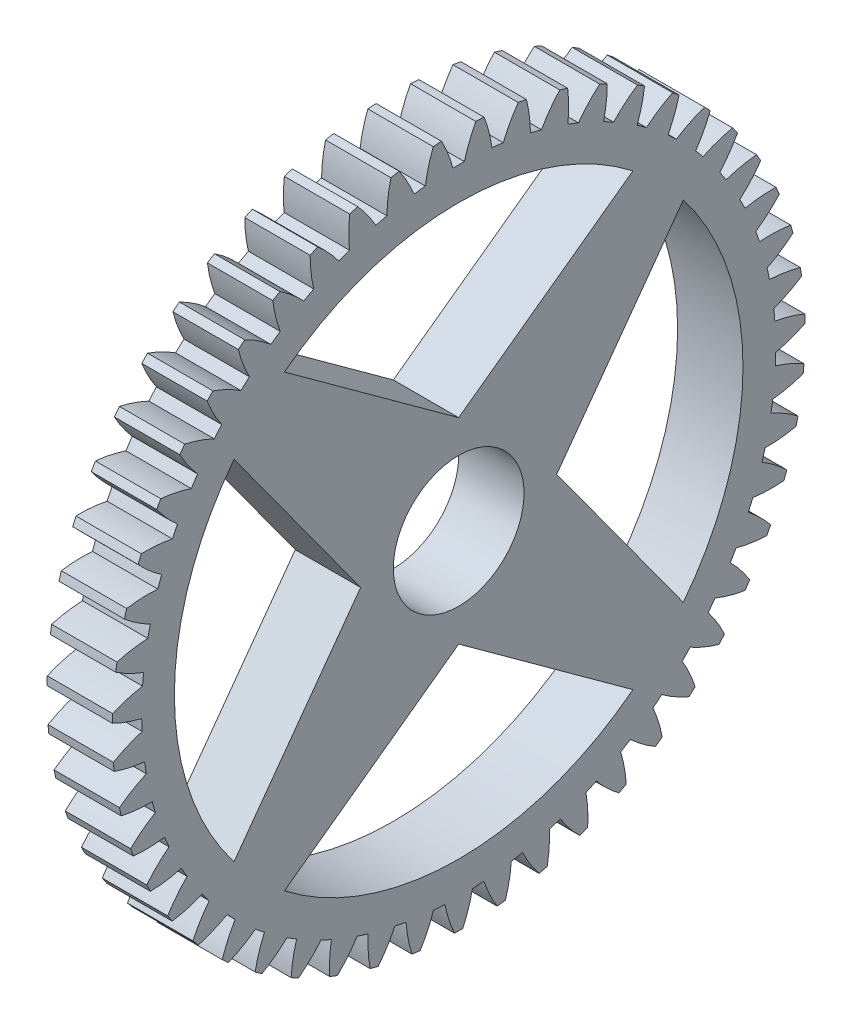
SolidWorks part; units mm, degrees
ref_plane "Plane1" through (0, 0, 0) normal (0, 0, 1) x (1, 0, 0)
ref_plane "Plane2" through (0, 0, 0) normal (0, 1, 0) x (1, 0, 0)
ref_plane "Plane3" through (0, 0, 0) normal (1, 0, 0) x (0, 0, -1)
sketch "HoldingSke" plane through (0, 0, 0) normal (0, 1, 0) x (1, 0, 0)
  line L0 (0, 0) -> (0.6293, -0.7771)
  line L1 (-15, 0) -> (100, 0) construction
  line L2 (0, 0) -> (-2.1039, 2.3779)
  line L3 (0, 0) -> (-11.863, 4.5341)
  line L4 (0, 0) -> (5.4348, 6.7114)
  line L5 (0, 0) -> (-46.8476, -17.4728)
  line L6 (0, 0) -> (-4.1448, -2.7965)
  line L7 (-2.1039, 2.3779) -> (8.6586, 51.2059)
  line L8 (-76.2, 54.61) -> (-75.3, 54.61)
  line L9 (-71.009, 38.7566) -> (-53.1078, 45.2721)
  line L10 (-76.2, 71.12) -> (104.1128, 71.12)
  line L11 (0, 0) -> (-5, 0)
  line L12 (-76.2, 101.6) -> (-76.162, 101.6)
  line L13 (24.9733, 27.94) -> (52.9518, 28.4284)
  line L14 (24.9733, 27.94) -> (24.9743, 27.94)
  line L15 (24.9733, 27.94) -> (100.4006, 29.5858)
  line L16 (-63.627, -1) -> (-12.827, -1)
  circle A0 centre (0, 0) radius 2.5
  circle A1 centre (0, 0) radius 24.249
  circle A2 centre (0, 0) radius 37.5
  circle A3 centre (0, 0) radius 2.5
sketch "BasProSke" plane through (0, 0, 0) normal (0, 1, 0) x (1, 0, 0)
  line L0 (-10, 0) -> (60, 0) construction
  line L1 (0, 0) -> (0, 26.5)
  line L2 (0, 0) -> (5, 0)
  line L3 (5, 0) -> (5, 26.5)
  line L4 (5, 26.5) -> (0, 26.5)
revolve "Base-Revolve" add sketch "BasProSke" angle 360 about L0
sketch "TooCutSke" plane through (0, 0, 0) normal (1, 0, 0) x (0, 0, -1)
  line L1 (0, 0) -> (0, 107) construction
  line L2 (0, 0) -> (-0.8518, 25.4858) construction
  line L3 (0, 0) -> (-3.1384, 50.883) construction
  line L4 (-0.8518, 25.4858) -> (-1.5692, 25.4415) construction
  arc A0 (0.4368, 24.2451) -> (-0.4368, 24.2451) centre (0, 0) ccw
  arc A1 (1.3275, 26.4922) -> (-1.3275, 26.4922) centre (0, 0) ccw
  circle A2 centre (0, 0) radius 25.5 construction
  circle A3 centre (0, 0) radius 23.9622 construction
  arc A4 (-0.4368, 24.2451) -> (-1.3275, 26.4922) centre (-10.2976, 21.6366) ccw
  arc A5 (1.3275, 26.4922) -> (0.4368, 24.2451) centre (10.2976, 21.6366) ccw
extrude "ToothCut" cut sketch "TooCutSke" along normal through all
fillet "Breaks" [suppressed] radius 0.02
fillet "RootFillets" [suppressed] radius 0.251
pattern_circular "TeethCuts" count 51 every 7.059 about axis through (-10, 0, 0) along (1, 0, 0) of "ToothCut", "RootFillets", "Breaks"
sketch "HubNeaOneSke" plane through (0, 0, 0) normal (-1, 0, 0) x (0, 0, 1)
  circle A0 centre (0, 0) radius 24.249
extrude "HubNearOne" [suppressed] add sketch "HubNeaOneSke" along normal blind 45.0001
sketch "HubNeaBotSke" plane through (0, 0, 0) normal (-1, 0, 0) x (0, 0, 1)
  circle A0 centre (0, 0) radius 24.249
extrude "HubNearBoth" [suppressed] add sketch "HubNeaBotSke" along normal blind 22.5
ref_plane "FarPln" through (5, 0, 0) normal (1, 0, 0) x (0, 0, -1)
sketch "HubFarSke" plane through (5, 0, 0) normal (1, 0, 0) x (0, 0, -1)
  circle A0 centre (0, 0) radius 24.249
extrude "HubFar" [suppressed] add sketch "HubFarSke" along normal blind 22.5
sketch "BorSke" plane through (0, 0, 0) normal (1, 0, 0) x (0, 0, -1)
  circle A0 centre (0, 0) radius 2.5
extrude "Bore" cut sketch "BorSke" along normal mid plane 100.0001
sketch "KeySke" plane through (0, 0, 0) normal (1, 0, 0) x (0, 0, -1)
  line L0 (-1, 0) -> (-1, 3.4)
  line L1 (-1, 3.4) -> (1, 3.4)
  line L2 (1, 3.4) -> (1, 0)
  line L3 (0, 0) -> (0, 34) construction
  line L4 (-1, 0) -> (1, 0)
extrude "Keyway" [suppressed] cut sketch "KeySke" along normal mid plane 100.0001
pattern_circular "Keyway2" [suppressed] count 2 every 90 about axis through (-10, 0, 0) along (1, 0, 0)
sketch "Sketch1" plane through (5, 0, 0) normal (1, 0, 0) x (0, 0, -1)
  line L0 (1.5, 2) -> (1.5, -2)
  circle A0 centre (0, 0) radius 2.5
  dimension "D1" = 5
  dimension "D2" = 1.5
extrude "Boss-Extrude1" add sketch "Sketch1" against normal blind 5 contours L0 A0
sketch "Sketch2" plane through (0, 0, 0) normal (-1, 0, 0) x (0, 0, 1)
  line L0 (0, -7.5) -> (13.3302, -17.185)
  line L1 (7.5, 7.5) -> (-7.5, 7.5)
  line L2 (7.5, 7.5) -> (7.5, -7.5)
  line L3 (7.5, -7.5) -> (-7.5, -7.5)
  line L4 (-7.5, 7.5) -> (-7.5, -7.5)
  line L5 (7.5, 7.5) -> (-7.5, -7.5) construction
  line L6 (7.5, -7.5) -> (-7.5, 7.5) construction
  line L7 (0, -7.5) -> (-13.3302, -17.185)
  line L8 (-7.5, 0) -> (-17.185, -13.3302)
  line L9 (-7.5, 0) -> (-17.185, 13.3302)
  line L10 (0, 7.5) -> (-13.3302, 17.185)
  line L11 (0, 7.5) -> (13.3302, 17.185)
  line L12 (7.5, 0) -> (17.185, 13.3302)
  line L13 (7.5, 0) -> (17.185, -13.3302)
  line L14 (0, -1000) -> (0, 49000) construction
  line L15 (-1000, 0) -> (49000, 0) construction
  circle A0 centre (0, 0) radius 24.249 construction
  circle A1 centre (0, 0) radius 5
  circle A2 centre (0, 0) radius 21.749
  point P21 (-17.2553, -13.3909)
  dimension "D1" = 10
  dimension "D2" = 2.5
  dimension "D3" = 15
  dimension "D4" = 108
  dimension "D5" = 108
  dimension "D6" = 108
  dimension "D7" = 108
  dimension "D8" = 54
  dimension "D9" = 54
  dimension "D10" = 54
  dimension "D11" = 54
extrude "Cut-Extrude1" cut sketch "Sketch2" against normal through all both and the other way through all contours L13 A2 L12 | L11 A2 L10 | L9 A2 L8 | L7 A2 L0 | A1
equation "' \"Module@HoldingSke\" = 6.35"
equation "' \"Num_teeth@HoldingSke\" = 12"
equation "' \"Ap@HoldingSke\" =  20"
equation "' \"Ap@HoldingSke\" = 20"
equation "' \"Width@HoldingSke\" = 0.5 * 25.4"
equation "' \"Hub_dia@HoldingSke\"= 1 * 25.4"
equation "' \"Hub_dia@HoldingSke\" = 1 * 25.4"
equation "' \"Overall_len@HoldingSke\" = 1.0 * 25.4"
equation "' \"Bore@HoldingSke\" = 0.75 * 25.4"
equation "' \"T_dim@HoldingSke\" = 0.1 * 25.4"
equation "' \"Width@KeySke\" = 0.25 * 25.4"
equation "' \"Show_teeth@HoldingSke\" = 13"
equation "' \"Backlash@HoldingSke\" = 0.009 * 25.4"
equation "' \"Addendum_fac@HoldingSke\" = 1.0"
equation "' \"Dedendum_fac@HoldingSke\" = 1.25"
equation "' \"Dedendum_add@HoldingSke\" = 0.00005 * 25.4"
equation "' \"Clearance_fac@HoldingSke\" = 0.25"
equation "\"Pitch@HoldingSke\" = 1 / \"Module@HoldingSke\""
equation "\"Overcut_dia@TooCutSke\" = (\"Num_teeth@HoldingSke\" + 2 * \"Addendum_fac@HoldingSke\") / \"Pitch@HoldingSke\" + 0.002 * 25.4"
equation "\"Pitch_dia@TooCutSke\" = \"Num_teeth@HoldingSke\" / \"Pitch@HoldingSke\""
equation "\"Base_dia@TooCutSke\" = \"Num_teeth@HoldingSke\" / \"Pitch@HoldingSke\" * cos((\"Ap@HoldingSke\"  * 3.14159265 / 180))"
equation "\"Root_dia@TooCutSke\" = (\"Num_teeth@HoldingSke\" + 2) / \"Pitch@HoldingSke\" - 2 * (\"Addendum_fac@HoldingSke\" + \"Dedendum_fac@HoldingSke\") / \"Pitch@HoldingSke\" - \"Dedendum_add@HoldingSke\" * 2"
equation "\"Half_ang@TooCutSke\" = 180 / \"Num_teeth@HoldingSke\""
equation "\"Half_CT@TooCutSke\" = \"Num_teeth@HoldingSke\" / \"Pitch@HoldingSke\" * sin((3.14159265 / 2 / \"Num_teeth@HoldingSke\")) / 2 - 7 * \"Backlash@HoldingSke\" / 4"
equation "\"Flank_rad@TooCutSke\" = \"Num_teeth@HoldingSke\" / \"Pitch@HoldingSke\" / 5"
equation "\"Radius@RootFillets\" = \"Clearance_fac@HoldingSke\" / \"Pitch@HoldingSke\" + \"Dedendum_add@HoldingSke\""
equation "\"Break_rad@Breaks\" = 0.02 / \"Pitch@HoldingSke\""
equation "\"Thickness@HoldingSke\" = \"Width@HoldingSke\""
equation "\"OAL@HoldingSke\" = \"Thickness@HoldingSke\""
equation "\"MHD@HoldingSke\" = (\"Num_teeth@HoldingSke\" + 2) / \"Pitch@HoldingSke\" - 2 * (\"Addendum_fac@HoldingSke\" + \"Dedendum_fac@HoldingSke\")  / \"Pitch@HoldingSke\" - \"Dedendum_add@HoldingSke\" * 2"
equation "\"MBD@HoldingSke\" = (\"Num_teeth@HoldingSke\" + 2) / \"Pitch@HoldingSke\" - 2 * (\"Addendum_fac@HoldingSke\" + \"Dedendum_fac@HoldingSke\")  / \"Pitch@HoldingSke\" - \"Dedendum_add@HoldingSke\" * 2 - 0.002 * 25.4"
equation "\"MHD@HoldingSke\" = ((sgn( \"MHD@HoldingSke\" - \"Hub_dia@HoldingSke\" )-1)*( \"MHD@HoldingSke\" - \"Hub_dia@HoldingSke\" ))/-2+ \"Hub_dia@HoldingSke\""
equation "\"MBD@HoldingSke\" = ((sgn( \"MBD@HoldingSke\" - \"Bore@HoldingSke\" )-1)*( \"MBD@HoldingSke\" - \"Bore@HoldingSke\" ))/-2+ \"Bore@HoldingSke\""
equation "\"OAL@HoldingSke\" = ((sgn( \"OAL@HoldingSke\" - \"Overall_len@HoldingSke\" )+1)*( \"OAL@HoldingSke\" - \"Overall_len@HoldingSke\" ))/2 + \"Overall_len@HoldingSke\" + 0.000002 * 25.4"
equation "\"Num_teeth@TeethCuts\" = int( \"Show_teeth@HoldingSke\" ) + 1"
equation "\"Num_teeth@TeethCuts\" = ((sgn( \"Num_teeth@TeethCuts\" - \"Num_teeth@HoldingSke\" )-1)*( \"Num_teeth@TeethCuts\" - \"Num_teeth@HoldingSke\" ))/-2+ \"Num_teeth@HoldingSke\""
equation "\"Num_teeth@TeethCuts\" = ((sgn( \"Num_teeth@TeethCuts\" - 2.0)+1)*( \"Num_teeth@TeethCuts\" - 2.0))/2 +2.0"
equation "\"Angle@TeethCuts\" = 360.0 / \"Num_teeth@HoldingSke\""
equation "\"Diameter@BasProSke\" = (\"Num_teeth@HoldingSke\" + 2 * \"Addendum_fac@HoldingSke\") / \"Pitch@HoldingSke\""
equation "\"Thickness@BasProSke\"  = \"Thickness@HoldingSke\""
equation "' \"Fillet_rad@BasProSke\" =  \"Thickness@HoldingSke\" * 0.05"
equation "' \"Fillet_rad@BasProSke\" = \"Thickness@HoldingSke\" * 0.05"
equation "\"MHD@HoldingSke\" = ((sgn( \"MHD@HoldingSke\" - \"Root_dia@TooCutSke\" )-1)*( \"MHD@HoldingSke\" - \"Root_dia@TooCutSke\" ))/-2+ \"Root_dia@TooCutSke\""
equation "\"Diameter@HubNeaOneSke\" = \"MHD@HoldingSke\""
equation "\"Length@HubNearOne\" = \"OAL@HoldingSke\" - \"Thickness@BasProSke\""
equation "\"Diameter@HubNeaBotSke\" = \"MHD@HoldingSke\""
equation "\"Length@HubNearBoth\" = ( \"OAL@HoldingSke\" - \"Thickness@BasProSke\" ) / 2.0"
equation "\"Thickness@FarPln\" = \"Thickness@BasProSke\""
equation "\"Diameter@HubFarSke\" = \"MHD@HoldingSke\""
equation "\"Length@HubFar\" = ( \"OAL@HoldingSke\" - \"Thickness@BasProSke\" ) / 2.0"
equation "\"Diameter@BorSke\" = \"MBD@HoldingSke\""
equation "\"D1@Bore\" = \"OAL@HoldingSke\" * 2.0"
equation "\"D1@Keyway\" = \"OAL@HoldingSke\" * 2.0"
equation "\"Offset@KeySke\" = \"T_dim@HoldingSke\" + \"MBD@HoldingSke\" / 2.0"
